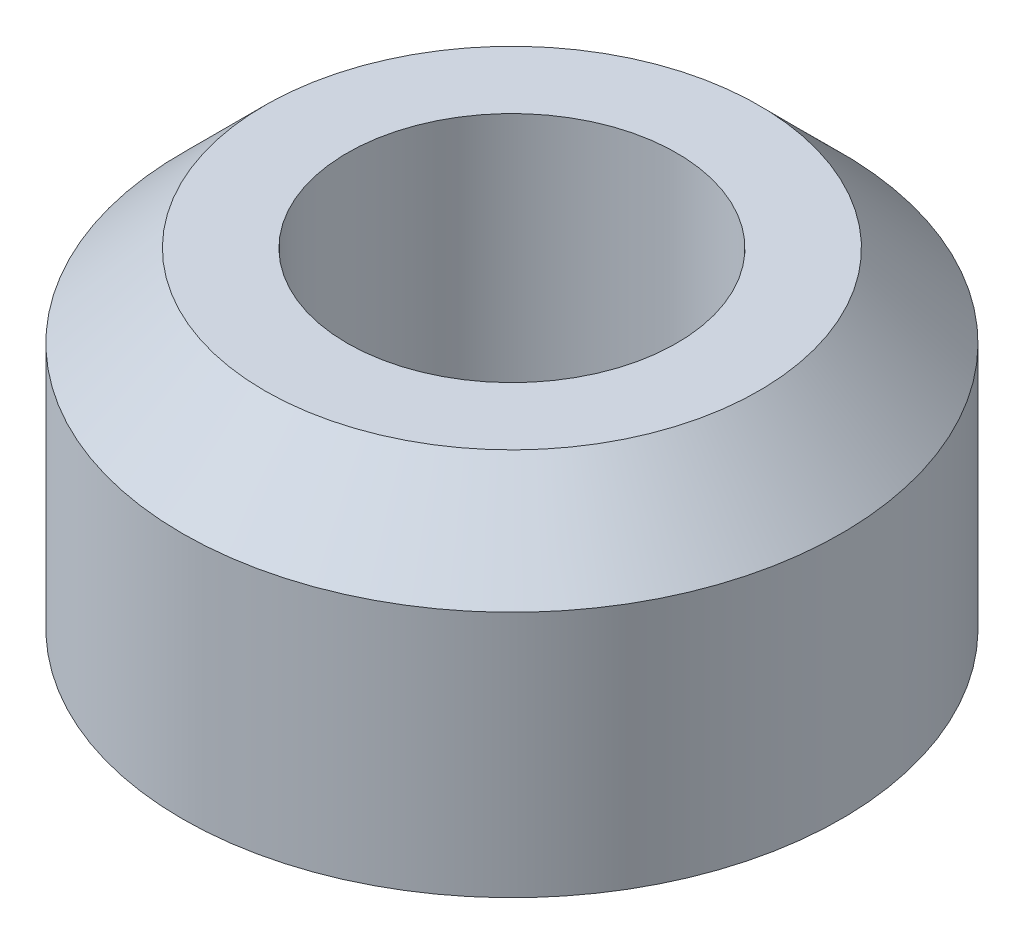
SolidWorks part; units mm, degrees
ref_plane "Front Plane" through (0, 0, 0) normal (0, 0, 1) x (1, 0, 0)
ref_plane "Top Plane" through (0, 0, 0) normal (0, 1, 0) x (1, 0, 0)
ref_plane "Right Plane" through (0, 0, 0) normal (1, 0, 0) x (0, 0, -1)
sketch "Sketch1" plane through (0, 0, 0) normal (0, 0, 1) x (1, 0, 0)
  line L0 (3.175, 0) -> (6.35, 0)
  line L1 (6.35, 0) -> (6.35, 4.7625)
  line L2 (6.35, 4.7625) -> (4.7625, 6.35)
  line L3 (4.7625, 6.35) -> (3.175, 6.35)
  line L4 (0, 6.35) -> (0, 0) construction
  line L5 (0, 3.175) -> (3.175, 3.175) construction
  line L6 (3.175, 0) -> (3.175, 6.35) construction
  line L7 (3.175, 0) -> (3.175, 6.35)
  point P11 (3.175, 3.175)
  point P12 (3.175, 3.175)
  dimension "D1" = 1.5875
  dimension "D2" = 1.5875
  dimension "D3" = 4.7625
  dimension "D4" = 6.35
  dimension "D5" = 6.35
  dimension "D6" = 3.175
revolve "Revolve1" add sketch "Sketch1" angle 360 about L4
